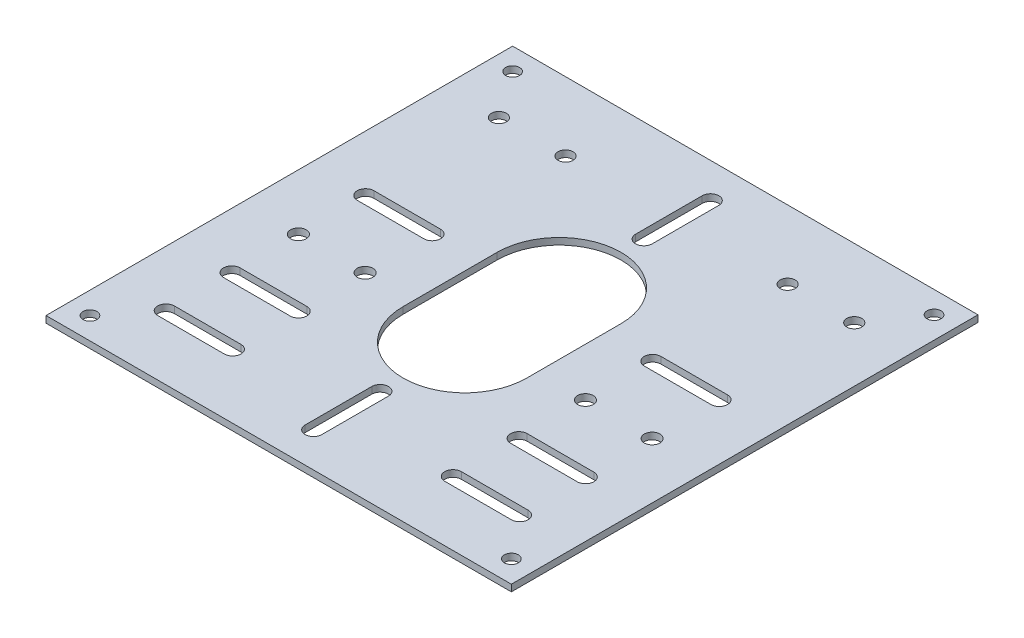
SolidWorks part; units mm, degrees
ref_plane "Front Plane" through (0, 0, 0) normal (0, 0, 1) x (1, 0, 0)
ref_plane "Top Plane" through (0, 0, 0) normal (0, 1, 0) x (1, 0, 0)
ref_plane "Right Plane" through (0, 0, 0) normal (1, 0, 0) x (0, 0, -1)
sketch "Sketch1" plane through (0, 0, 0) normal (0, 1, 0) x (1, 0, 0)
  line L0 (0, -11.3) -> (0, 11.3) construction
  line L1 (-55.85, 56) -> (55.85, 56)
  line L2 (-55.85, 56) -> (-55.85, -56)
  line L3 (-55.85, -56) -> (55.85, -56)
  line L4 (55.85, 56) -> (55.85, -56)
  line L5 (-55.85, 56) -> (55.85, -56) construction
  line L6 (-55.85, -56) -> (55.85, 56) construction
  line L7 (-14.85, -11.3) -> (-14.85, 11.3)
  line L8 (14.85, -11.3) -> (14.85, 11.3)
  arc A0 (-14.85, -11.3) -> (14.85, -11.3) centre (0, -11.3) ccw
  arc A1 (14.85, 11.3) -> (-14.85, 11.3) centre (0, 11.3) ccw
  point P0 (0, 0)
  point P8 (0, 0)
  point P13 (0, 26.15)
  point P14 (0, -26.15)
  dimension "D3" = 29.7
  dimension "D1" = 111.7
  dimension "D2" = 112
  dimension "D4" = 52.3
extrude "Boss-Extrude1" add sketch "Sketch1" along normal blind 1.6
sketch "Sketch2" plane through (0, 1.6, 0) normal (0, 1, 0) x (1, 0, 0)
  line L0 (-55.85, 0) -> (-39.4088, 0) construction
  line L1 (-55.85, 56) -> (-55.85, -56) construction
  line L2 (0, 26.15) -> (0, 45.5469) construction
  line L3 (0, 47.65) -> (0, 31.65) construction
  line L4 (2, 47.65) -> (2, 31.65)
  line L5 (-2, 47.65) -> (-2, 31.65)
  line L7 (0, -47.65) -> (0, -31.65) construction
  line L8 (2, -47.65) -> (2, -31.65)
  line L9 (-2, -47.65) -> (-2, -31.65)
  arc A0 (14.85, 11.3) -> (-14.85, 11.3) centre (0, 11.3) ccw construction
  arc A1 (2, 47.65) -> (-2, 47.65) centre (0, 47.65) ccw
  arc A2 (-2, 31.65) -> (2, 31.65) centre (0, 31.65) ccw
  arc A3 (2, -47.65) -> (-2, -47.65) centre (0, -47.65) cw
  arc A4 (-2, -31.65) -> (2, -31.65) centre (0, -31.65) cw
  point P13 (0, 39.65)
  point P18 (0, 29.65)
  point P19 (0, 49.65)
  point P22 (0, -39.65)
  dimension "D2" = 20
  dimension "D1" = 3.5
  dimension "D3" = 4
extrude "Cut-Extrude1" cut sketch "Sketch2" against normal blind 1.6
sketch "Sketch3" plane through (0, 1.6, 0) normal (0, 1, 0) x (1, 0, 0)
  line L0 (0, 56) -> (0, 53.6572) construction
  line L1 (55.85, 56) -> (-55.85, 56) construction
  line L2 (-42.45, -40.6) -> (-26.45, -40.6) construction
  line L3 (-55.85, 56) -> (-55.85, -56) construction
  line L4 (-55.85, 0) -> (-44.7107, 0) construction
  line L5 (-42.45, 7.3) -> (-26.45, 7.3) construction
  line L6 (-42.45, 9.3) -> (-26.45, 9.3)
  line L7 (-42.45, 5.3) -> (-26.45, 5.3)
  line L8 (-42.45, -38.6) -> (-26.45, -38.6)
  line L9 (-42.45, -42.6) -> (-26.45, -42.6)
  line L10 (-42.45, -24.8) -> (-26.45, -24.8) construction
  line L11 (-42.45, -22.8) -> (-26.45, -22.8)
  line L12 (-42.45, -26.8) -> (-26.45, -26.8)
  line L13 (-55.85, -56) -> (55.85, -56) construction
  line L14 (42.45, -40.6) -> (26.45, -40.6) construction
  line L15 (42.45, -38.6) -> (26.45, -38.6)
  line L16 (42.45, -42.6) -> (26.45, -42.6)
  line L17 (42.45, -24.8) -> (26.45, -24.8) construction
  line L18 (42.45, -22.8) -> (26.45, -22.8)
  line L19 (42.45, -26.8) -> (26.45, -26.8)
  line L20 (42.45, 7.3) -> (26.45, 7.3) construction
  line L21 (42.45, 9.3) -> (26.45, 9.3)
  line L22 (42.45, 5.3) -> (26.45, 5.3)
  line L23 (-42.45, -8.825) -> (-26.45, -8.825) construction
  line L24 (-42.65, 39.5) -> (-26.65, 39.5) construction
  line L25 (-42.45, 7.3) -> (-42.45, -40.6) construction
  line L26 (-26.45, 7.3) -> (-26.45, -40.6) construction
  line L27 (-26.45, 7.2347) -> (-26.45, -40.6653) construction
  circle A0 centre (-50.575, 50.725) radius 1.675
  circle A1 centre (50.575, 50.725) radius 1.675
  circle A2 centre (50.575, -50.725) radius 1.675
  circle A3 centre (-50.575, -50.725) radius 1.675
  circle A4 centre (-42.65, 39.5) radius 1.8
  circle A5 centre (-26.65, 39.5) radius 1.8
  arc A6 (-42.45, 9.3) -> (-42.45, 5.3) centre (-42.45, 7.3) ccw
  arc A7 (-26.45, 5.3) -> (-26.45, 9.3) centre (-26.45, 7.3) ccw
  arc A8 (-42.45, -38.6) -> (-42.45, -42.6) centre (-42.45, -40.6) ccw
  arc A9 (-26.45, -42.6) -> (-26.45, -38.6) centre (-26.45, -40.6) ccw
  arc A10 (-42.45, -22.8) -> (-42.45, -26.8) centre (-42.45, -24.8) ccw
  arc A11 (-26.45, -26.8) -> (-26.45, -22.8) centre (-26.45, -24.8) ccw
  circle A12 centre (-42.45, -8.825) radius 1.875
  circle A13 centre (-26.45, -8.825) radius 1.875
  arc A14 (42.45, -38.6) -> (42.45, -42.6) centre (42.45, -40.6) cw
  arc A15 (26.45, -42.6) -> (26.45, -38.6) centre (26.45, -40.6) cw
  arc A16 (42.45, -22.8) -> (42.45, -26.8) centre (42.45, -24.8) cw
  arc A17 (26.45, -26.8) -> (26.45, -22.8) centre (26.45, -24.8) cw
  circle A18 centre (26.45, -8.825) radius 1.875
  circle A19 centre (42.45, -8.825) radius 1.875
  arc A20 (42.45, 9.3) -> (42.45, 5.3) centre (42.45, 7.3) cw
  arc A21 (26.45, 5.3) -> (26.45, 9.3) centre (26.45, 7.3) cw
  circle A22 centre (42.65, 39.5) radius 1.8
  circle A23 centre (26.65, 39.5) radius 1.8
  point P9 (-50.575, 52.4)
  point P10 (-52.25, 50.725)
  point P21 (-44.45, 39.5)
  point P22 (-42.65, 41.3)
  point P25 (-26.65, 41.3)
  point P28 (-34.45, 7.3)
  point P36 (-34.45, -40.6)
  point P43 (-34.45, -24.8)
  point P50 (-44.325, -8.825)
  point P53 (-28.45, 39.5)
  point P58 (-28.325, -8.825)
  point P60 (0, 0)
  point P61 (0, 0)
  point P62 (-42.45, -10.7)
  point P64 (-26.45, -10.7)
  point P66 (34.45, -40.6)
  point P73 (34.45, -24.8)
  point P84 (34.45, 7.3)
  point P93 (0, 0)
  point P96 (0, 0)
  dimension "D1" = 101.15
  dimension "D3" = 3.35
  dimension "D4" = 32.2
  dimension "D7" = 15.8
  dimension "D12" = 16
  dimension "D13" = 3.75
  dimension "D8" = 13.2
  dimension "D10" = 3.6
  dimension "D11" = 3.6
  dimension "D14" = 3.75
  dimension "D2" = 101.45
  dimension "D5" = 16.125
  dimension "D6" = 15.975
  dimension "D9" = 16.5
  dimension "D15" = 4
  dimension "D16" = 4
  dimension "D17" = 4
  dimension "D18" = 13.4
  dimension "D19" = 16
  dimension "D20" = 13.4
extrude "Cut-Extrude2" cut sketch "Sketch3" against normal blind 1.6
